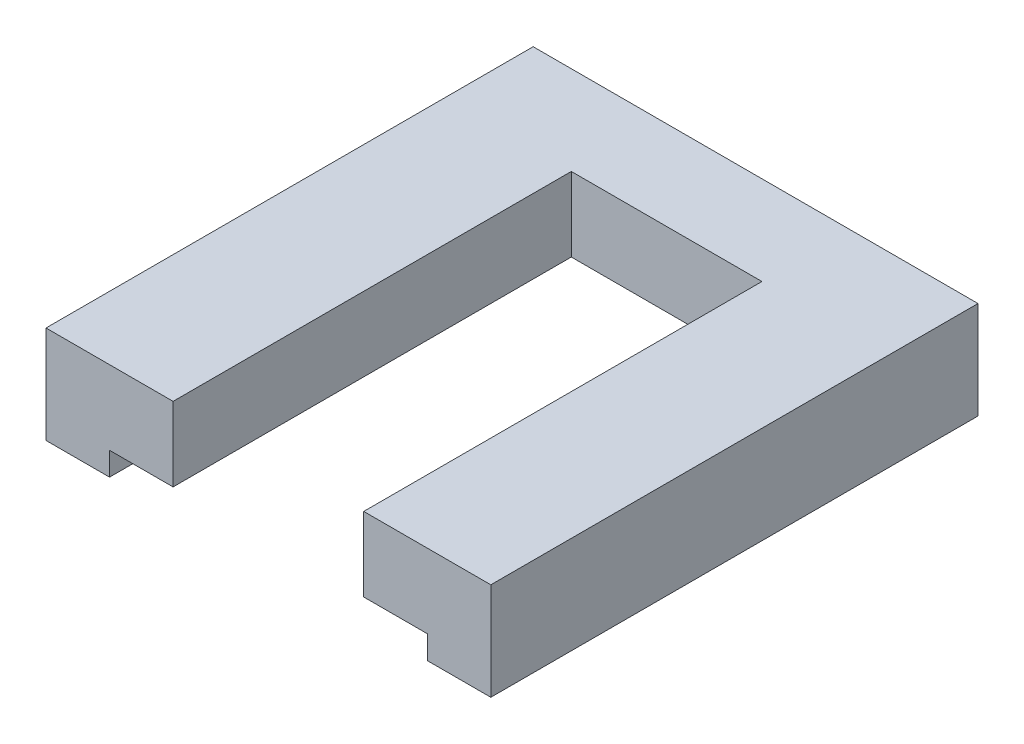
SolidWorks part; units mm, degrees
ref_plane "Front Plane" through (0, 0, 0) normal (0, 0, 1) x (1, 0, 0)
ref_plane "Top Plane" through (0, 0, 0) normal (0, 1, 0) x (1, 0, 0)
ref_plane "Right Plane" through (0, 0, 0) normal (1, 0, 0) x (0, 0, -1)
sketch "Sketch1" plane through (0, 0, 0) normal (0, 1, 0) x (1, 0, 0)
  line L0 (-11.2941, 13.5) -> (9.7059, 13.5)
  line L1 (-8.2941, 10.5) -> (6.7059, 10.5)
  line L2 (-8.2941, 10.5) -> (-8.2941, -9.5)
  line L4 (6.7059, 10.5) -> (6.7059, -9.5)
  line L5 (9.7059, 13.5) -> (9.7059, -10.085)
  line L6 (6.7059, -9.5) -> (11.1176, -9.5)
  line L7 (-11.2941, 13.5) -> (-11.2941, -9.5)
  line L8 (-11.2941, -9.5) -> (-8.2941, -9.5)
  line L9 (11.1176, -9.5) -> (9.7059, -10.085)
  line L10 (-11.2941, 13.5) -> (-11.2941, -12.5) construction
  line L11 (-11.2941, -12.5) -> (9.7059, -12.5) construction
  line L12 (9.7059, 13.5) -> (9.7059, -12.5) construction
  line L13 (-8.2941, -9.5) -> (6.7059, -9.5) construction
  dimension "D1" = 15
  dimension "D2" = 20
  dimension "D3" = 3
extrude "Boss-Extrude1" add sketch "Sketch1" along normal blind 1.1 contours L7 L8 L2 L1 L4 L6 L5 L0
sketch "Sketch2" plane through (0, 1.1, 0) normal (0, 1, 0) x (1, 0, 0)
  line L0 (-8.2941, -9.5) -> (-5.2941, -9.5)
  line L1 (-5.2941, -9.5) -> (-5.2941, 9.3)
  line L2 (-5.2941, 9.3) -> (3.7059, 9.3)
  line L3 (3.7059, 9.3) -> (3.7059, -9.5)
  line L4 (3.7059, -9.5) -> (6.7059, -9.5)
  line L5 (-0.7941, 15.3173) -> (-0.7941, -14.2112) construction
  line L6 (-8.2941, 10.5) -> (6.7059, 10.5) construction
  line L8 (-11.2941, 13.5) -> (-11.2941, -9.5)
  line L9 (-11.2941, -9.5) -> (-8.2941, -9.5)
  line L10 (-8.2941, -9.5) -> (-8.2941, 10.5)
  line L11 (-8.2941, 10.5) -> (6.7059, 10.5)
  line L12 (6.7059, 10.5) -> (6.7059, -9.5)
  line L13 (6.7059, -9.5) -> (9.7059, -9.5)
  line L14 (9.7059, -9.5) -> (9.7059, 13.5)
  line L15 (9.7059, 13.5) -> (-11.2941, 13.5)
  line L16 (-11.2941, 13.5) -> (-11.2941, -9.5)
  line L17 (-11.2941, -9.5) -> (-8.2941, -9.5)
  line L21 (6.7059, -9.5) -> (9.7059, -9.5)
  line L22 (9.7059, -9.5) -> (9.7059, 13.5)
  line L23 (9.7059, 13.5) -> (-11.2941, 13.5)
  dimension "D2" = 10.5
  dimension "D3" = 9
  dimension "D4" = 4.5
  dimension "D5" = 1.2
  dimension "D1" = 0
extrude "Boss-Extrude2" add sketch "Sketch2" along normal blind 3.5
